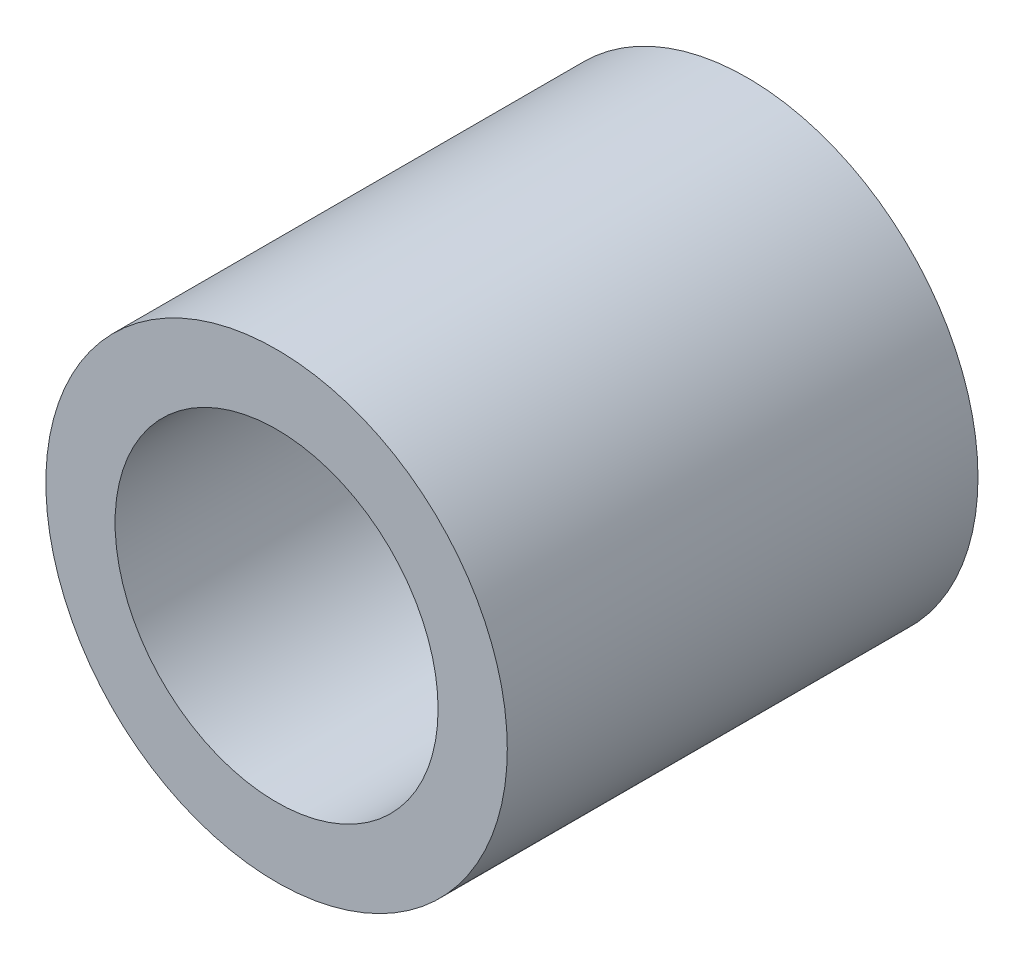
SolidWorks part; units mm, degrees
material "Brass"
ref_plane "Front" through (0, 0, 0) normal (0, 0, 1) x (1, 0, 0)
ref_plane "Top" through (0, 0, 0) normal (0, 1, 0) x (1, 0, 0)
ref_plane "Right" through (0, 0, 0) normal (1, 0, 0) x (0, 0, -1)
sketch "Sketch1" plane through (0, 0, 0) normal (0, 0, 1) x (1, 0, 0)
  circle A0 centre (0, 0) radius 17.5
  circle A1 centre (0, 0) radius 25
  dimension "D1" = 35
  dimension "D2" = 50
extrude "Boss-Extrude1" add sketch "Sketch1" along normal blind 51
